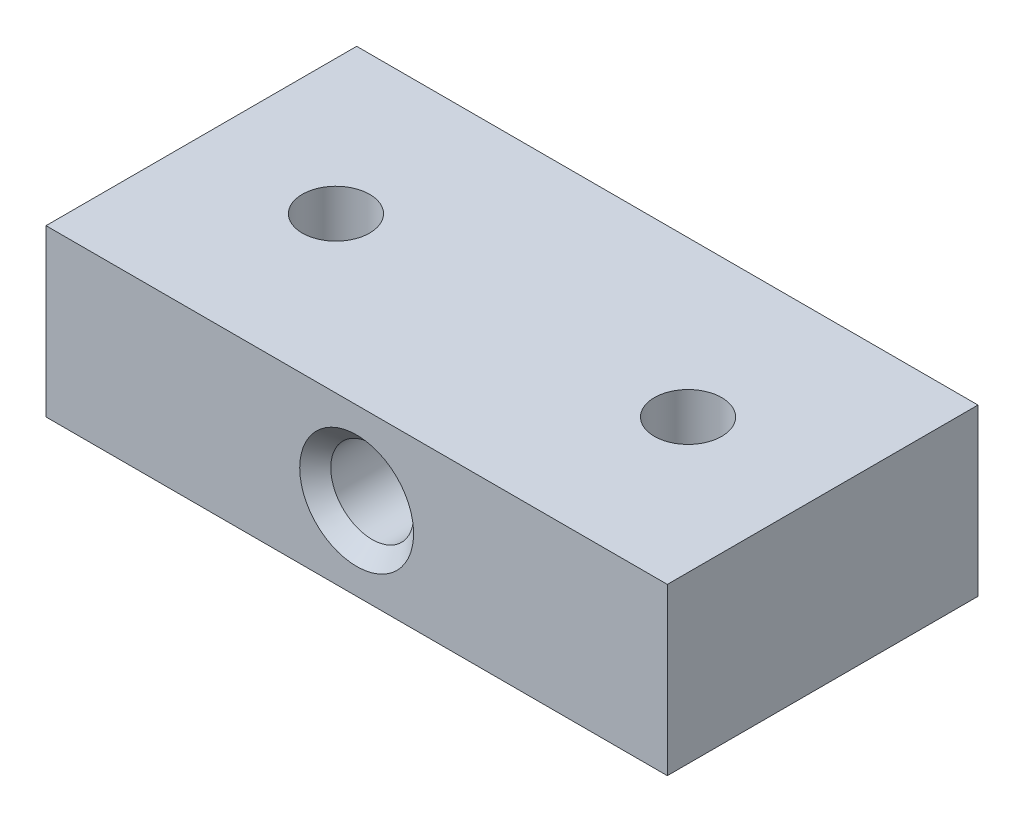
SolidWorks part; units mm, degrees
material "ABS PC"
ref_plane "Front Plane" through (0, 0, 0) normal (0, 0, 1) x (1, 0, 0)
ref_plane "Top Plane" through (0, 0, 0) normal (0, 1, 0) x (1, 0, 0)
ref_plane "Right Plane" through (0, 0, 0) normal (1, 0, 0) x (0, 0, -1)
sketch "Sketch1" plane through (0, 0, 0) normal (0, 1, 0) x (1, 0, 0)
  line L1 (0, 0) -> (60, 0)
  line L2 (0, 0) -> (0, 30)
  line L3 (0, 30) -> (60, 30)
  line L4 (60, 0) -> (60, 30)
  circle A0 centre (13, 15) radius 3.25
  circle A1 centre (47, 15) radius 3.25
  dimension "D3" = 6.5
  dimension "D5" = 13
  dimension "D6" = 15
  dimension "D1" = 30
  dimension "D2" = 60
  dimension "D4" = 13
extrude "Boss-Extrude1" add sketch "Sketch1" along normal blind 16
sketch "Sketch2" plane through (0, 0, 0) normal (0, 0, 1) x (1, 0, 0)
  line L0 (60, 16) -> (60, 0) construction
  line L1 (0, 0) -> (60, 0) construction
  circle A0 centre (30, 8) radius 4
  dimension "D1" = 8
  dimension "D2" = 30
  dimension "D3" = 8
extrude "Cut-Extrude1" cut sketch "Sketch2" against normal through all
chamfer "Chamfer1" distance 1.5 angle 45 2 edges at (34, 8, -30) (34, 8, 0)
